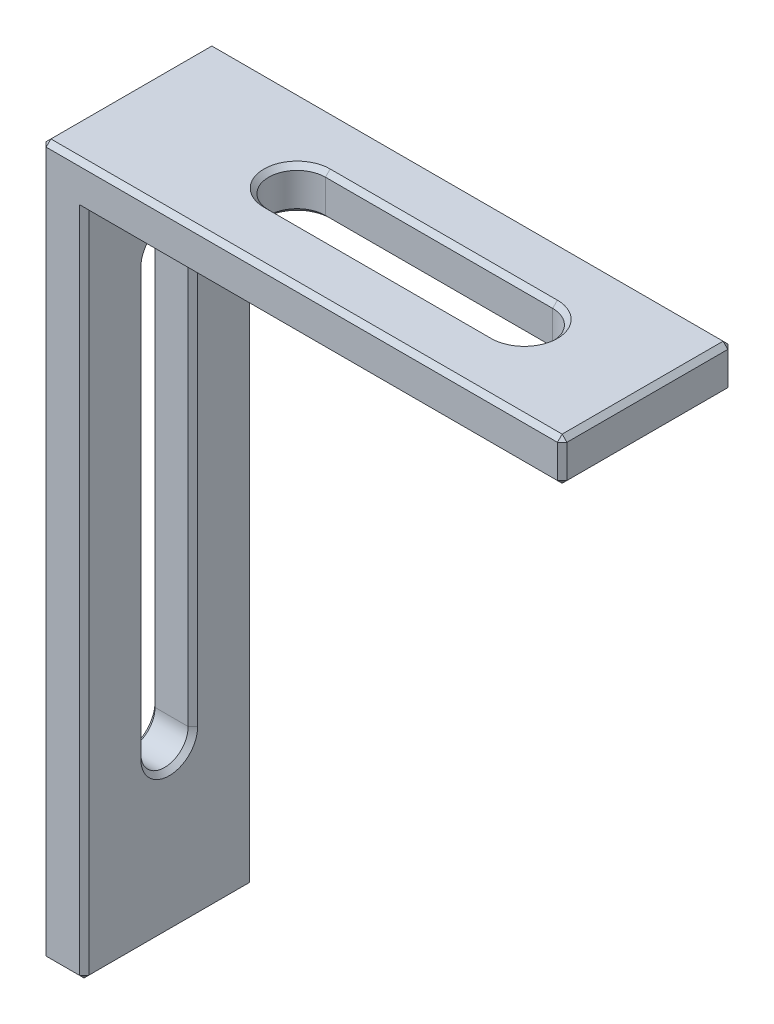
SolidWorks part; units mm, degrees
ref_plane "Plan de face" through (0, 0, 0) normal (0, 0, 1) x (1, 0, 0)
ref_plane "Plan de dessus" through (0, 0, 0) normal (0, 1, 0) x (1, 0, 0)
ref_plane "Plan de droite" through (0, 0, 0) normal (1, 0, 0) x (0, 0, -1)
sketch "Esquisse1" plane through (0, 0, 0) normal (0, 0, 1) x (1, 0, 0)
  line L0 (0, 0) -> (0, 150)
  line L1 (0, 150) -> (110, 150)
  line L2 (110, 150) -> (110, 141)
  line L3 (110, 141) -> (9, 141)
  line L4 (9, 141) -> (9, 0)
  line L5 (9, 0) -> (0, 0)
  dimension "D1" = 9
  dimension "D2" = 9
  dimension "D3" = 150
  dimension "D4" = 110
extrude "Boss.-Extru.1" add sketch "Esquisse1" along normal blind 36
sketch "Esquisse2" plane through (0, 0, 0) normal (-1, 0, 0) x (0, 0, 1)
  line L0 (18, 142.7381) -> (18, -18.2094) construction
  line L1 (23, 125) -> (23, 35)
  line L2 (13, 125) -> (13, 35)
  line L3 (36, 0) -> (0, 0) construction
  arc A0 (23, 125) -> (13, 125) centre (18, 125) ccw
  arc A1 (13, 35) -> (23, 35) centre (18, 35) ccw
  dimension "D1" = 10
  dimension "D2" = 90
  dimension "D3" = 35
extrude "Enlèv. mat.-Extru.1" cut sketch "Esquisse2" against normal blind 36
sketch "Esquisse3" plane through (0, 150, 0) normal (0, 1, 0) x (1, 0, 0)
  line L0 (-4.5066, -18) -> (134.2806, -18) construction
  line L1 (0, -36) -> (0, 0) construction
  line L2 (36, -12) -> (84, -12)
  line L3 (36, -24) -> (84, -24)
  line L5 (110, 0) -> (0, 0) construction
  arc A0 (36, -12) -> (36, -24) centre (36, -18) ccw
  arc A1 (84, -24) -> (84, -12) centre (84, -18) ccw
  dimension "D1" = 12
  dimension "D2" = 36
  dimension "D3" = 48
  dimension "D4" = 12
extrude "Enlèv. mat.-Extru.2" cut sketch "Esquisse3" against normal blind 36
chamfer "Chanfrein1" distance 1 angle 45 33 edges at (4.5, 0, 36) (9, 0, 18) (4.5, 0, 0) (0, 0, 18) (0, 75, 0) (0, 75, 36) (9, 70.5, 36) (59.5, 141, 36) (9, 70.5, 0) (59.5, 141, 0) (110, 145.5, 0) (110, 141, 18) (110, 145.5, 36) (110, 150, 18) (55, 150, 0) (0, 150, 18) (55, 150, 36) (0, 30, 18) (0, 80, 23) (0, 130, 18) (0, 80, 13) (9, 30, 18) (9, 80, 23) (9, 130, 18) (9, 80, 13) (90, 141, 18) (60, 141, 24) (60, 141, 12) (30, 141, 18) (60, 150, 24) (30, 150, 18) (60, 150, 12) (90, 150, 18)
